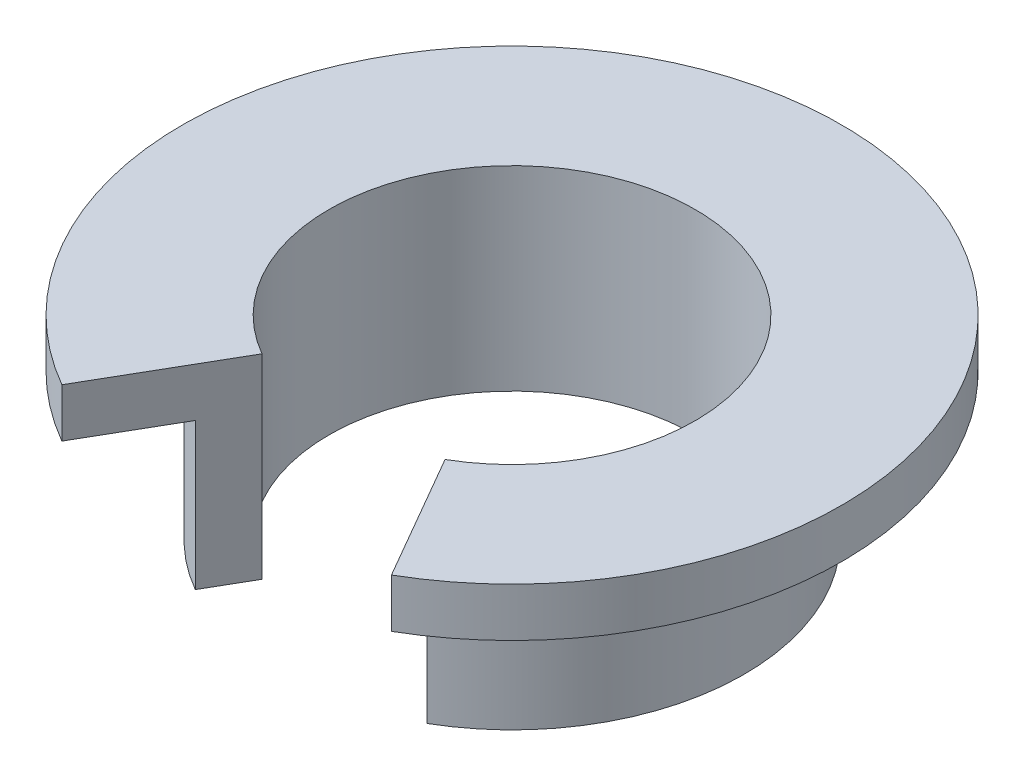
SolidWorks part; units mm, degrees
ref_plane "Front Plane" through (0, 0, 0) normal (0, 0, 1) x (1, 0, 0)
ref_plane "Top Plane" through (0, 0, 0) normal (0, 1, 0) x (1, 0, 0)
ref_plane "Right Plane" through (0, 0, 0) normal (1, 0, 0) x (0, 0, -1)
sketch "Sketch1" plane through (0, 0, 0) normal (0, 0, 1) x (1, 0, 0)
  line L0 (0, 0) -> (0, 12.4335) construction
  line L1 (7.5, 0) -> (7.5, 8)
  line L2 (7.5, 8) -> (13.5, 8)
  line L3 (13.5, 8) -> (13.5, 6)
  line L4 (13.5, 6) -> (9.5, 6)
  line L5 (9.5, 6) -> (9.5, 0)
  line L6 (9.5, 0) -> (7.5, 0)
  dimension "D1" = 15
  dimension "D2" = 19
  dimension "D3" = 27
  dimension "D4" = 8
  dimension "D5" = 6
revolve "Revolve1" add sketch "Sketch1" angle 360 about L0
sketch "Sketch2" plane through (0, 0, 0) normal (0, 1, 0) x (1, 0, 0)
  line L0 (0, 0) -> (0, -18.6945) construction
  line L1 (-9.0912, -15.7464) -> (0, 0)
  line L2 (0, 0) -> (8.6255, -14.9399)
  line L3 (-9.0912, -15.7464) -> (8.6255, -14.9399)
  dimension "D1" = 30
  dimension "D2" = 30
extrude "Cut-Extrude1" cut sketch "Sketch2" along normal blind 10
scale "Scale1" scale about origin uniform scaling yes scale factor 0.5
